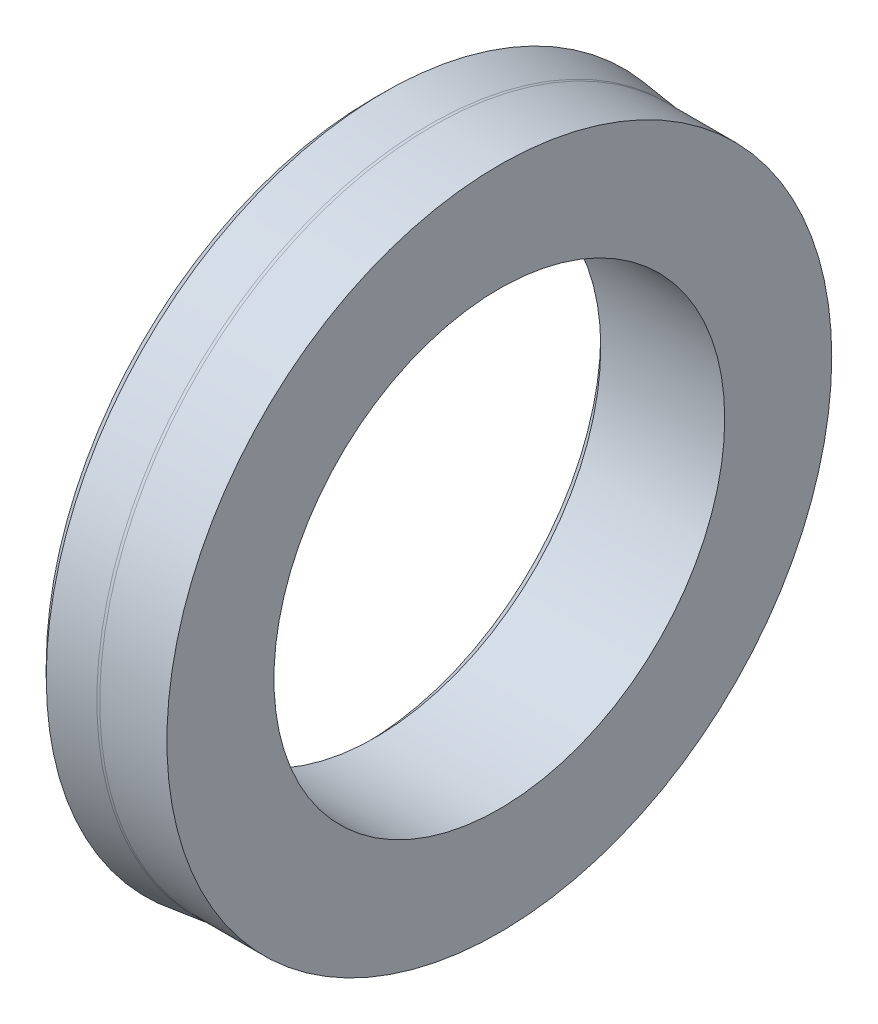
SolidWorks part; units mm, degrees
ref_plane "Front" through (0, 0, 0) normal (0, 0, 1) x (1, 0, 0)
ref_plane "Top" through (0, 0, 0) normal (0, 1, 0) x (1, 0, 0)
ref_plane "Right" through (0, 0, 0) normal (1, 0, 0) x (0, 0, -1)
curve "ImportedCurve1"
curve "ImportedCurve2"
curve "ImportedCurve3"
curve "ImportedCurve4"
curve "ImportedCurve5"
curve "ImportedCurve6"
curve "ImportedCurve7"
curve "ImportedCurve8"
curve "ImportedCurve9"
curve "ImportedCurve10"
curve "ImportedCurve11"
curve "ImportedCurve12"
curve "ImportedCurve13"
curve "ImportedCurve14"
curve "ImportedCurve15"
curve "ImportedCurve16"
curve "ImportedCurve17"
curve "ImportedCurve18"
curve "ImportedCurve19"
curve "ImportedCurve20"
curve "ImportedCurve21"
curve "ImportedCurve22"
curve "ImportedCurve23"
curve "ImportedCurve24"
curve "ImportedCurve25"
curve "ImportedCurve26"
curve "ImportedCurve27"
curve "ImportedCurve28"
curve "ImportedCurve29"
curve "ImportedCurve30"
curve "ImportedCurve31"
curve "ImportedCurve32"
sketch "Sketch1" plane through (0, 0, 0) normal (0, 0, 1) x (1, 0, 0)
  line L0 (596.9212, 446.5026) -> (581.157, 446.5026) construction
  line L1 (596.9212, 445.5026) -> (596.9212, 447.5026) construction
  line L2 (585.9212, 466.5026) -> (596.9212, 466.5026) construction
  line L3 (585.7212, 475.5026) -> (586.7212, 476.5026) construction
  line L4 (585.7212, 475.5026) -> (585.7212, 472.5953) construction
  line L5 (585.7212, 472.5953) -> (589.5031, 472.1318) construction
  line L6 (584.9212, 470.5026) -> (589.4036, 470.5026) construction
  line L7 (584.9212, 470.5026) -> (584.9212, 467.5026) construction
  line L8 (584.9212, 467.5026) -> (585.9212, 466.5026) construction
  line L9 (596.9212, 466.5026) -> (596.9212, 475.9976) construction
  line L10 (596.9212, 475.9976) -> (590.9645, 475.9976) construction
  line L11 (586.7212, 476.5026) -> (590.7213, 476.0125) construction
  line L12 (585.9212, 466.5026) -> (596.9212, 466.5026)
  line L13 (585.7212, 475.5026) -> (586.7212, 476.5026)
  line L14 (585.7212, 475.5026) -> (585.7212, 472.5953)
  line L15 (585.7212, 472.5953) -> (589.5031, 472.1318)
  line L16 (584.9212, 470.5026) -> (589.4036, 470.5026)
  line L17 (584.9212, 470.5026) -> (584.9212, 467.5026)
  line L18 (584.9212, 467.5026) -> (585.9212, 466.5026)
  line L19 (596.9212, 466.5026) -> (596.9212, 475.9976)
  line L20 (596.9212, 475.9976) -> (590.9645, 475.9976)
  line L21 (586.7212, 476.5026) -> (590.7213, 476.0125)
  spline S0 degree 3 poles (589.5031, 472.1318) (590.9472, 471.9549) (590.8586, 470.5026) (589.4036, 470.5026) knots 0 0 0 0 1 1 1 1 weights 1 0.373951 0.373951 1 construction
  spline S1 degree 3 poles (590.7213, 476.0125) (590.802, 476.0026) (590.8832, 475.9976) (590.9645, 475.9976) knots 0 0 0 0 1 1 1 1 weights 1 0.998761 0.998761 1 construction
  spline S2 degree 3 poles (589.5031, 472.1318) (590.9472, 471.9549) (590.8586, 470.5026) (589.4036, 470.5026) knots 0 0 0 0 1 1 1 1 weights 1 0.373951 0.373951 1
  spline S3 degree 3 poles (590.7213, 476.0125) (590.802, 476.0026) (590.8832, 475.9976) (590.9645, 475.9976) knots 0 0 0 0 1 1 1 1 weights 1 0.998761 0.998761 1
revolve "Revolve1" add sketch "Sketch1" angle 360 about L0
